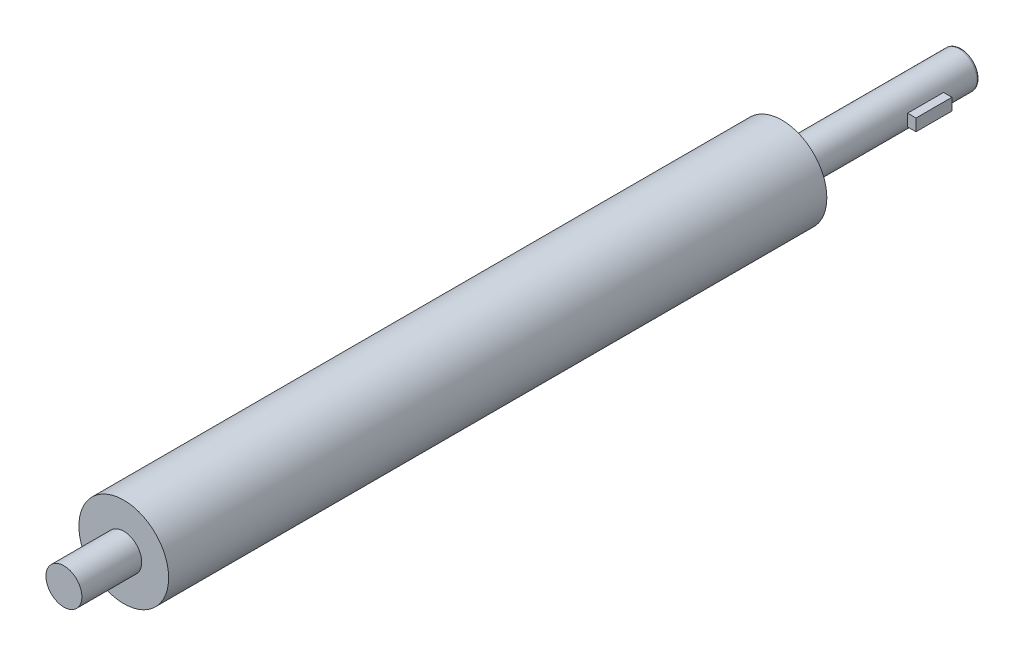
SolidWorks part; units mm, degrees
ref_plane "Front Plane" through (0, 0, 0) normal (0, 0, 1) x (1, 0, 0)
ref_plane "Top Plane" through (0, 0, 0) normal (0, 1, 0) x (1, 0, 0)
ref_plane "Right Plane" through (0, 0, 0) normal (1, 0, 0) x (0, 0, -1)
sketch "Sketch1" plane through (0, 0, 0) normal (0, 0, 1) x (1, 0, 0)
  circle A0 centre (0, 0) radius 37.5
  dimension "D1" = 75
extrude "Boss-Extrude1" add sketch "Sketch1" along normal blind 550
sketch "Sketch2" plane through (0, 0, 550) normal (0, 0, 1) x (1, 0, 0)
  circle A0 centre (0, 0) radius 15
  dimension "D1" = 30
extrude "Boss-Extrude2" add sketch "Sketch2" along normal blind 50
sketch "Sketch3" plane through (0, 0, 0) normal (0, 0, -1) x (-1, 0, 0)
  circle A0 centre (0, 0) radius 15
  dimension "D1" = 30
extrude "Boss-Extrude3" add sketch "Sketch3" along normal blind 150
ref_plane "Plane1" through (15, 0, 0) normal (1, 0, 0) x (0, 0, -1)
sketch "Sketch6" plane through (15, 0, 0) normal (1, 0, 0) x (0, 0, -1)
  line L0 (103.5113, 23.1932) -> (103.5113, -28.9842) construction
  line L1 (90, 5) -> (120, 5)
  line L2 (90, 5) -> (90, -5)
  line L3 (90, -5) -> (120, -5)
  line L4 (120, 5) -> (120, -5)
  line L5 (105, -5) -> (105, 5) construction
  line L6 (90, 0) -> (120, 0) construction
  line L7 (75, 15) -> (75, -15) construction
  line L8 (150, 15) -> (0, 15) construction
  line L9 (0, -15) -> (150, -15) construction
  point P0 (105, 0)
  dimension "D1" = 30
  dimension "D2" = 30
  dimension "D3" = 10
extrude "Boss-Extrude4" add sketch "Sketch6" along normal blind 7 separate body
fillet "Fillet1" radius 2 1 edges at (-15, 0, -150)
